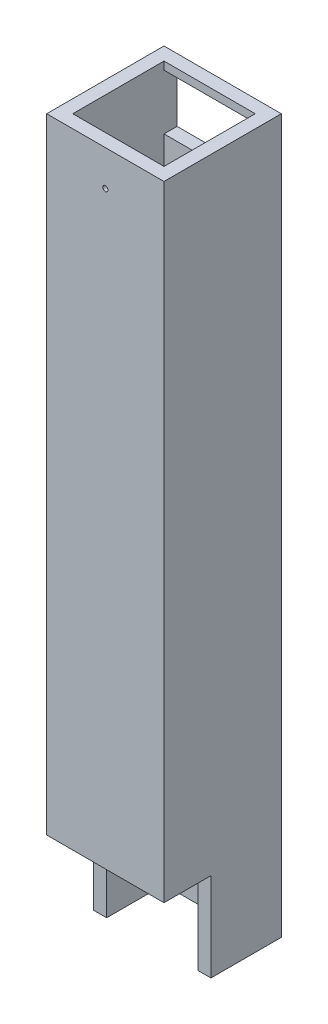
SolidWorks part; units mm, degrees
ref_plane "Alzado" through (0, 0, 0) normal (0, 0, 1) x (1, 0, 0)
ref_plane "Planta" through (0, 0, 0) normal (0, 1, 0) x (1, 0, 0)
ref_plane "Vista lateral" through (0, 0, 0) normal (1, 0, 0) x (0, 0, -1)
sketch "Croquis1" plane through (0, 0, 0) normal (0, 1, 0) x (1, 0, 0)
  line L1 (-22.5, -22.5) -> (22.5, -22.5)
  line L2 (-22.5, -22.5) -> (-22.5, 22.5)
  line L3 (-22.5, 22.5) -> (22.5, 22.5)
  line L4 (22.5, -22.5) -> (22.5, 22.5)
  line L5 (-22.5, -22.5) -> (22.5, 22.5) construction
  line L6 (-22.5, 22.5) -> (22.5, -22.5) construction
  point P0 (0, 0)
  dimension "D1" = 45
  dimension "D2" = 45
extrude "Saliente-Extruir1" add sketch "Croquis1" along normal blind 300
sketch "Croquis4" plane through (-22.5, 0, 0) normal (-1, 0, 0) x (0, 0, 1)
  line L1 (22.5, 300) -> (22.5, 0) construction
  line L3 (55, 0) -> (-55, 0) construction
  line L5 (4.5, 0) -> (4.5, 34)
  line L6 (4.5, 34) -> (22.5, 34)
  line L8 (22.5, 34) -> (22.5, 0)
  line L9 (22.5, 0) -> (4.5, 0)
  dimension "D4" = 34
extrude "Cortar-Extruir2" cut sketch "Croquis4" against normal through all
sketch "Croquis7" plane through (0, 0, 22.5) normal (0, 0, 1) x (1, 0, 0)
  line L0 (0, -24.75) -> (0, 24.75) construction
  line L1 (-22.5, 246.3879) -> (22.5, 246.3879)
  line L2 (-22.5, 246.3879) -> (-22.5, 273.6121)
  line L3 (-22.5, 273.6121) -> (22.5, 273.6121)
  line L4 (22.5, 246.3879) -> (22.5, 273.6121)
  line L5 (-22.5, 246.3879) -> (22.5, 273.6121) construction
  line L6 (-22.5, 273.6121) -> (22.5, 246.3879) construction
  line L7 (22.5, 300) -> (22.5, 34) construction
  point P0 (0, 260)
  dimension "D1" = 260
sketch "Croquis8" plane through (0, 300, 0) normal (0, 1, 0) x (1, 0, 0)
  line L0 (22.5, -22.5) -> (22.5, 22.5) construction
  line L1 (-17.5, -17.5) -> (17.5, -17.5)
  line L2 (-17.5, -17.5) -> (-17.5, 17.5)
  line L3 (-17.5, 17.5) -> (17.5, 17.5)
  line L4 (17.5, -17.5) -> (17.5, 17.5)
  line L5 (-17.5, -17.5) -> (17.5, 17.5) construction
  line L6 (-17.5, 17.5) -> (17.5, -17.5) construction
  line L7 (22.5, 22.5) -> (-22.5, 22.5) construction
  point P0 (0, 0)
  dimension "D1" = 5
  dimension "D2" = 5
extrude "Cortar-Extruir3" cut sketch "Croquis8" against normal through all contours L3 L4 L1 L2
sketch "Croquis9" plane through (0, 0, -22.5) normal (0, 0, -1) x (-1, 0, 0)
  line L0 (22.5, 273.6121) -> (-22.5, 246.3879) construction
  line L1 (-17.5, 249.4128) -> (17.5, 249.4128)
  line L2 (-17.5, 249.4128) -> (-17.5, 270.5872)
  line L3 (-17.5, 270.5872) -> (17.5, 270.5872)
  line L4 (17.5, 249.4128) -> (17.5, 270.5872)
  line L5 (-17.5, 249.4128) -> (17.5, 270.5872) construction
  line L6 (-17.5, 270.5872) -> (17.5, 249.4128) construction
  line L7 (22.5, 246.3879) -> (22.5, 273.6121) construction
  point P0 (0, 260)
  point P10 (22.5, 260)
  dimension "D1" = 5
extrude "Cortar-Extruir4" cut sketch "Croquis9" against normal blind 10 contours L4 L3 L2 L1
sketch "Croquis10" plane through (0, 0, 22.5) normal (0, 0, 1) x (1, 0, 0)
  circle A0 centre (0, 260) radius 1
  dimension "D1" = 2
extrude "Cortar-Extruir5" cut sketch "Croquis10" against normal blind 10
sketch "Croquis11" plane through (0, 0, 22.5) normal (0, 0, 1) x (1, 0, 0)
  line L0 (22.5, 300) -> (22.5, 34) construction
  line L1 (-22.5, 300) -> (22.5, 300)
  line L2 (-22.5, 300) -> (-22.5, 273.6121)
  line L3 (-22.5, 273.6121) -> (22.5, 273.6121)
  line L4 (22.5, 300) -> (22.5, 273.6121)
  line L5 (-22.5, 273.6121) -> (22.5, 273.6121) construction
  dimension "D1" = 0
extrude "Cortar-Extruir6" cut sketch "Croquis11" against normal through all
sketch "Croquis12" plane through (0, 0, 22.5) normal (0, 0, 1) x (1, 0, 0)
  line L0 (-22.5, 267.3717) -> (22.5, 246.3879)
  line L1 (-22.5, 246.3879) -> (-22.5, 273.6121) construction
  line L2 (-22.5, 246.3879) -> (22.5, 246.3879) construction
  dimension "D1" = 25
